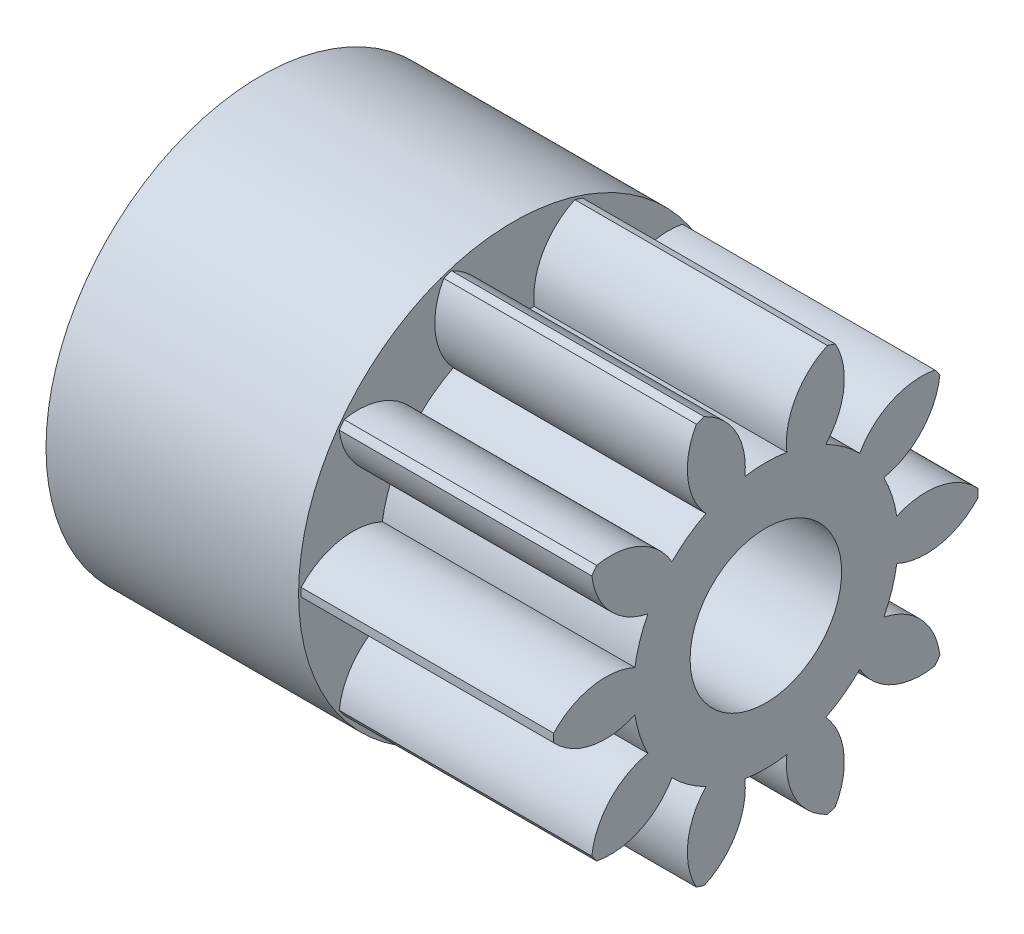
SolidWorks part; units mm, degrees
ref_plane "Plane1" through (0, 0, 0) normal (0, 0, 1) x (1, 0, 0)
ref_plane "Plane2" through (0, 0, 0) normal (0, 1, 0) x (1, 0, 0)
ref_plane "Plane3" through (0, 0, 0) normal (1, 0, 0) x (0, 0, -1)
sketch "HoldingSke" plane through (0, 0, 0) normal (0, 1, 0) x (1, 0, 0)
  line L0 (0, 0) -> (1.4069, -0.2481)
  line L1 (-15, 0) -> (100, 0) construction
  line L2 (0, 0) -> (-2.1039, 2.3779)
  line L3 (0, 0) -> (-11.863, 4.5341)
  line L4 (0, 0) -> (8.5048, 1.4996)
  line L5 (0, 0) -> (-46.8476, -17.4728)
  line L6 (0, 0) -> (-4.1448, -2.7965)
  line L7 (-2.1039, 2.3779) -> (8.6586, 51.2059)
  line L8 (-76.2, 54.61) -> (-75.7, 54.61)
  line L9 (-71.009, 38.7566) -> (-53.1078, 45.2721)
  line L10 (-76.2, 71.12) -> (104.1128, 71.12)
  line L11 (0, 0) -> (-5, 0)
  line L12 (-76.2, 101.6) -> (-76.173, 101.6)
  line L13 (24.9733, 27.94) -> (52.9518, 28.4284)
  line L14 (24.9733, 27.94) -> (24.9743, 27.94)
  line L15 (24.9733, 27.94) -> (100.4006, 29.5858)
  line L16 (-63.627, -0.7) -> (-12.827, -0.7)
  circle A0 centre (0, 0) radius 1.5
  circle A1 centre (0, 0) radius 2.624
  circle A2 centre (0, 0) radius 37.5
  circle A3 centre (0, 0) radius 1.5
  dimension "MHD" = 5.248
  dimension "Hub_dia" = 75
  dimension "Bore" = 3
  dimension "MBD" = 3
  dimension "Num_teeth" = 10
  dimension "Pitch" = 1.4286
  dimension "Overall_len" = 50
  dimension "Show_teeth" = 10
  dimension "Thickness" = 5
  dimension "OAL" = 50.0001
  dimension "T_dim" = 0.5
  dimension "Ap" = 20
  dimension "H" = 19.05
  dimension "Pitch_radius" = 180.3128
  dimension "Width" = 5
  dimension "Backlash" = 0.027
  dimension "Addendum_fac" = 1
  dimension "Dedendum_fac" = 1.25
  dimension "Clearance_fac" = 0.25
  dimension "Dedendum_add" = 0.001
  dimension "Module" = 0.7
sketch "BasProSke" plane through (0, 0, 0) normal (0, 1, 0) x (1, 0, 0)
  line L0 (-10, 0) -> (60, 0) construction
  line L1 (0, 0) -> (0, 4.2)
  line L2 (0, 0) -> (5, 0)
  line L3 (5, 0) -> (5, 4.2)
  line L4 (5, 4.2) -> (0, 4.2)
  dimension "Thickness" = 5
  dimension "Diameter" = 8.4
revolve "Base-Revolve" add sketch "BasProSke" angle 360 about L0
sketch "TooCutSke" plane through (0, 0, 0) normal (1, 0, 0) x (0, 0, -1)
  line L1 (0, 0) -> (0, 107) construction
  line L2 (0, 0) -> (-0.5947, 3.4491) construction
  line L3 (0, 0) -> (-2.1409, 6.589) construction
  line L4 (-0.5947, 3.4491) -> (-1.0705, 3.2945) construction
  arc A0 (0.4155, 2.5909) -> (-0.4155, 2.5909) centre (0, 0) ccw
  arc A1 (1.2546, 4.0349) -> (-1.2546, 4.0349) centre (0, 0) ccw
  circle A2 centre (0, 0) radius 3.5 construction
  circle A3 centre (0, 0) radius 3.2889 construction
  arc A4 (-0.4155, 2.5909) -> (-1.2546, 4.0349) centre (-1.8066, 2.7483) ccw
  arc A5 (1.2546, 4.0349) -> (0.4155, 2.5909) centre (1.8066, 2.7483) ccw
  dimension "Root_dia" = 5.248
  dimension "Overcut_dia" = 8.4508
  dimension "Pitch_dia" = 7
  dimension "Base_dia" = 6.5778
  dimension "Flank_rad" = 1.4
  dimension "Half_ang" = 18
  dimension "Half_CT" = 0.5003
extrude "ToothCut" cut sketch "TooCutSke" along normal through all
fillet "Breaks" [suppressed] radius 0.014
fillet "RootFillets" [suppressed] radius 0.176
pattern_circular "TeethCuts" count 10 every 36 about axis through (-10, 0, 0) along (1, 0, 0) of "ToothCut", "RootFillets", "Breaks"
sketch "HubNeaOneSke" plane through (0, 0, 0) normal (-1, 0, 0) x (0, 0, 1)
  circle A0 centre (0, 0) radius 2.624
  dimension "Diameter" = 5.248
extrude "HubNearOne" [suppressed] add sketch "HubNeaOneSke" along normal blind 45.0001
sketch "HubNeaBotSke" plane through (0, 0, 0) normal (-1, 0, 0) x (0, 0, 1)
  circle A0 centre (0, 0) radius 2.624
  dimension "Diameter" = 5.248
extrude "HubNearBoth" [suppressed] add sketch "HubNeaBotSke" along normal blind 22.5
ref_plane "FarPln" through (5, 0, 0) normal (1, 0, 0) x (0, 0, -1)
sketch "HubFarSke" plane through (5, 0, 0) normal (1, 0, 0) x (0, 0, -1)
  circle A0 centre (0, 0) radius 2.624
  dimension "Diameter" = 5.248
extrude "HubFar" [suppressed] add sketch "HubFarSke" along normal blind 22.5
sketch "BorSke" plane through (0, 0, 0) normal (1, 0, 0) x (0, 0, -1)
  circle A0 centre (0, 0) radius 1.5
  dimension "Diameter" = 3
extrude "Bore" cut sketch "BorSke" along normal mid plane 100.0001
sketch "KeySke" plane through (0, 0, 0) normal (1, 0, 0) x (0, 0, -1)
  line L0 (-0.6, 0) -> (-0.6, 2)
  line L1 (-0.6, 2) -> (0.6, 2)
  line L2 (0.6, 2) -> (0.6, 0)
  line L3 (0, 0) -> (0, 34) construction
  line L4 (-0.6, 0) -> (0.6, 0)
  dimension "Offset" = 2
  dimension "Width" = 1.2
extrude "Keyway" [suppressed] cut sketch "KeySke" along normal mid plane 100.0001
pattern_circular "Keyway2" [suppressed] count 2 every 90 about axis through (-10, 0, 0) along (1, 0, 0)
sketch "Croquis1" plane through (0, 0, 0) normal (-1, 0, 0) x (0, 0, 1)
  circle A0 centre (0, 0) radius 4.25
  circle A1 centre (0, 0) radius 3.25
  dimension "D1" = 8.5
  dimension "D2" = 6.5
extrude "Saliente-Extruir1" add sketch "Croquis1" along normal blind 5
sketch "Croquis2" plane through (0, 0, 0) normal (-1, 0, 0) x (0, 0, 1)
  circle A0 centre (0, 0) radius 3.25
  circle A1 centre (0, 0) radius 3.25 construction
extrude "Saliente-Extruir2" add sketch "Croquis2" along normal blind 2
sketch "Croquis3" plane through (-2, 0, 0) normal (-1, 0, 0) x (0, 0, 1)
  line L0 (-1.95, 2.6) -> (-1.95, -2.6)
  circle A0 centre (0, 0) radius 3.25 construction
  circle A1 centre (0, 0) radius 3.25 construction
  arc A2 (-1.95, 2.6) -> (-1.95, -2.6) centre (0, 0) ccw
  dimension "D1" = 5.2
extrude "Saliente-Extruir3" add sketch "Croquis3" along normal blind 2
equation "' \"Module@HoldingSke\" = 6.35"
equation "' \"Num_teeth@HoldingSke\" = 12"
equation "' \"Ap@HoldingSke\" =  20"
equation "' \"Ap@HoldingSke\" = 20"
equation "' \"Width@HoldingSke\" = 0.5 * 25.4"
equation "' \"Hub_dia@HoldingSke\"= 1 * 25.4"
equation "' \"Hub_dia@HoldingSke\" = 1 * 25.4"
equation "' \"Overall_len@HoldingSke\" = 1.0 * 25.4"
equation "' \"Bore@HoldingSke\" = 0.75 * 25.4"
equation "' \"T_dim@HoldingSke\" = 0.1 * 25.4"
equation "' \"Width@KeySke\" = 0.25 * 25.4"
equation "' \"Show_teeth@HoldingSke\" = 13"
equation "' \"Backlash@HoldingSke\" = 0.009 * 25.4"
equation "' \"Addendum_fac@HoldingSke\" = 1.0"
equation "' \"Dedendum_fac@HoldingSke\" = 1.25"
equation "' \"Dedendum_add@HoldingSke\" = 0.00005 * 25.4"
equation "' \"Clearance_fac@HoldingSke\" = 0.25"
equation "\"Pitch@HoldingSke\" = 1 / \"Module@HoldingSke\""
equation "\"Overcut_dia@TooCutSke\" = (\"Num_teeth@HoldingSke\" + 2 * \"Addendum_fac@HoldingSke\") / \"Pitch@HoldingSke\" + 0.002 * 25.4"
equation "\"Pitch_dia@TooCutSke\" = \"Num_teeth@HoldingSke\" / \"Pitch@HoldingSke\""
equation "\"Base_dia@TooCutSke\" = \"Num_teeth@HoldingSke\" / \"Pitch@HoldingSke\" * cos((\"Ap@HoldingSke\"  * 3.14159265 / 180))"
equation "\"Root_dia@TooCutSke\" = (\"Num_teeth@HoldingSke\" + 2) / \"Pitch@HoldingSke\" - 2 * (\"Addendum_fac@HoldingSke\" + \"Dedendum_fac@HoldingSke\") / \"Pitch@HoldingSke\" - \"Dedendum_add@HoldingSke\" * 2"
equation "\"Half_ang@TooCutSke\" = 180 / \"Num_teeth@HoldingSke\""
equation "\"Half_CT@TooCutSke\" = \"Num_teeth@HoldingSke\" / \"Pitch@HoldingSke\" * sin((3.14159265 / 2 / \"Num_teeth@HoldingSke\")) / 2 - 7 * \"Backlash@HoldingSke\" / 4"
equation "\"Flank_rad@TooCutSke\" = \"Num_teeth@HoldingSke\" / \"Pitch@HoldingSke\" / 5"
equation "\"Radius@RootFillets\" = \"Clearance_fac@HoldingSke\" / \"Pitch@HoldingSke\" + \"Dedendum_add@HoldingSke\""
equation "\"Break_rad@Breaks\" = 0.02 / \"Pitch@HoldingSke\""
equation "\"Thickness@HoldingSke\" = \"Width@HoldingSke\""
equation "\"OAL@HoldingSke\" = \"Thickness@HoldingSke\""
equation "\"MHD@HoldingSke\" = (\"Num_teeth@HoldingSke\" + 2) / \"Pitch@HoldingSke\" - 2 * (\"Addendum_fac@HoldingSke\" + \"Dedendum_fac@HoldingSke\")  / \"Pitch@HoldingSke\" - \"Dedendum_add@HoldingSke\" * 2"
equation "\"MBD@HoldingSke\" = (\"Num_teeth@HoldingSke\" + 2) / \"Pitch@HoldingSke\" - 2 * (\"Addendum_fac@HoldingSke\" + \"Dedendum_fac@HoldingSke\")  / \"Pitch@HoldingSke\" - \"Dedendum_add@HoldingSke\" * 2 - 0.002 * 25.4"
equation "\"MHD@HoldingSke\" = ((sgn( \"MHD@HoldingSke\" - \"Hub_dia@HoldingSke\" )-1)*( \"MHD@HoldingSke\" - \"Hub_dia@HoldingSke\" ))/-2+ \"Hub_dia@HoldingSke\""
equation "\"MBD@HoldingSke\" = ((sgn( \"MBD@HoldingSke\" - \"Bore@HoldingSke\" )-1)*( \"MBD@HoldingSke\" - \"Bore@HoldingSke\" ))/-2+ \"Bore@HoldingSke\""
equation "\"OAL@HoldingSke\" = ((sgn( \"OAL@HoldingSke\" - \"Overall_len@HoldingSke\" )+1)*( \"OAL@HoldingSke\" - \"Overall_len@HoldingSke\" ))/2 + \"Overall_len@HoldingSke\" + 0.000002 * 25.4"
equation "\"Num_teeth@TeethCuts\" = int( \"Show_teeth@HoldingSke\" ) + 1"
equation "\"Num_teeth@TeethCuts\" = ((sgn( \"Num_teeth@TeethCuts\" - \"Num_teeth@HoldingSke\" )-1)*( \"Num_teeth@TeethCuts\" - \"Num_teeth@HoldingSke\" ))/-2+ \"Num_teeth@HoldingSke\""
equation "\"Num_teeth@TeethCuts\" = ((sgn( \"Num_teeth@TeethCuts\" - 2.0)+1)*( \"Num_teeth@TeethCuts\" - 2.0))/2 +2.0"
equation "\"Angle@TeethCuts\" = 360.0 / \"Num_teeth@HoldingSke\""
equation "\"Diameter@BasProSke\" = (\"Num_teeth@HoldingSke\" + 2 * \"Addendum_fac@HoldingSke\") / \"Pitch@HoldingSke\""
equation "\"Thickness@BasProSke\"  = \"Thickness@HoldingSke\""
equation "' \"Fillet_rad@BasProSke\" =  \"Thickness@HoldingSke\" * 0.05"
equation "' \"Fillet_rad@BasProSke\" = \"Thickness@HoldingSke\" * 0.05"
equation "\"MHD@HoldingSke\" = ((sgn( \"MHD@HoldingSke\" - \"Root_dia@TooCutSke\" )-1)*( \"MHD@HoldingSke\" - \"Root_dia@TooCutSke\" ))/-2+ \"Root_dia@TooCutSke\""
equation "\"Diameter@HubNeaOneSke\" = \"MHD@HoldingSke\""
equation "\"Length@HubNearOne\" = \"OAL@HoldingSke\" - \"Thickness@BasProSke\""
equation "\"Diameter@HubNeaBotSke\" = \"MHD@HoldingSke\""
equation "\"Length@HubNearBoth\" = ( \"OAL@HoldingSke\" - \"Thickness@BasProSke\" ) / 2.0"
equation "\"Thickness@FarPln\" = \"Thickness@BasProSke\""
equation "\"Diameter@HubFarSke\" = \"MHD@HoldingSke\""
equation "\"Length@HubFar\" = ( \"OAL@HoldingSke\" - \"Thickness@BasProSke\" ) / 2.0"
equation "\"Diameter@BorSke\" = \"MBD@HoldingSke\""
equation "\"D1@Bore\" = \"OAL@HoldingSke\" * 2.0"
equation "\"D1@Keyway\" = \"OAL@HoldingSke\" * 2.0"
equation "\"Offset@KeySke\" = \"T_dim@HoldingSke\" + \"MBD@HoldingSke\" / 2.0"
